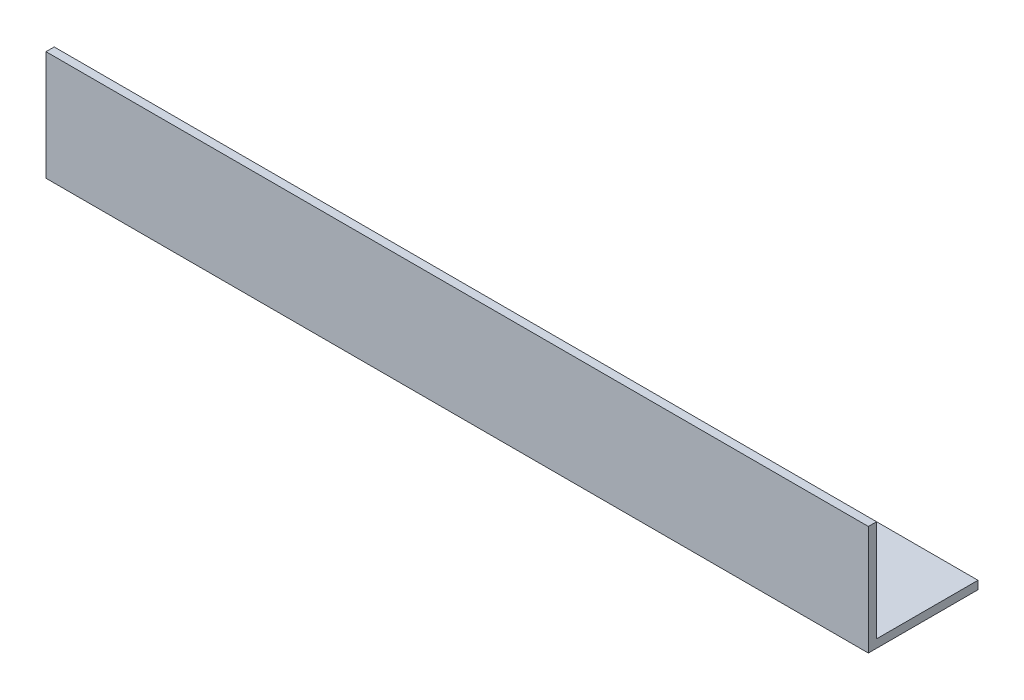
SolidWorks part; units mm, degrees
ref_plane "Спереди" through (0, 0, 0) normal (0, 0, 1) x (1, 0, 0)
ref_plane "Сверху" through (0, 0, 0) normal (0, 1, 0) x (1, 0, 0)
ref_plane "Справа" through (0, 0, 0) normal (1, 0, 0) x (0, 0, -1)
sketch "Эскиз1" plane through (0, 0, 0) normal (1, 0, 0) x (0, 0, -1)
  line L0 (0, 0) -> (0, 40)
  line L1 (0, 0) -> (40, 0)
extrude "Вытянуть-Тонкостенный1" add sketch "Эскиз1" along normal blind 300 thin
